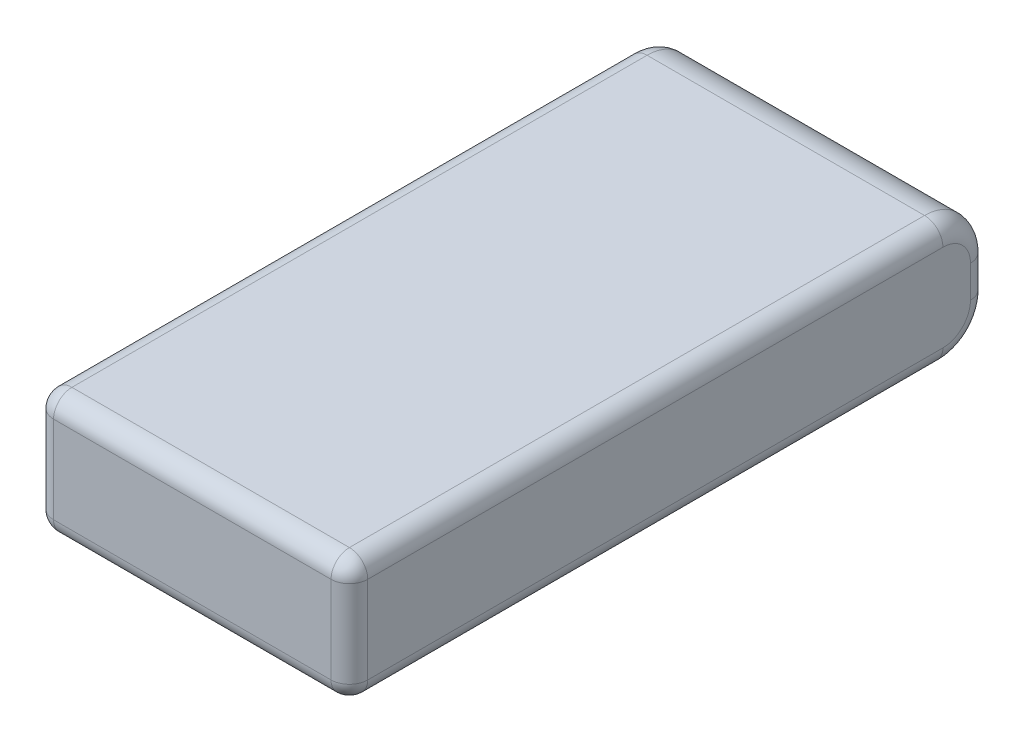
SolidWorks part; units mm, degrees
ref_plane "Front Plane" through (0, 0, 0) normal (0, 0, 1) x (1, 0, 0)
ref_plane "Top Plane" through (0, 0, 0) normal (0, 1, 0) x (1, 0, 0)
ref_plane "Right Plane" through (0, 0, 0) normal (1, 0, 0) x (0, 0, -1)
sketch "Sketch1" plane through (0, 0, 0) normal (0, 1, 0) x (1, 0, 0)
  line L1 (0, 0) -> (34.25, 0)
  line L2 (0, 0) -> (0, 69.7)
  line L3 (0, 69.7) -> (34.25, 69.7)
  line L4 (34.25, 0) -> (34.25, 69.7)
  dimension "D1" = 69.7
  dimension "D2" = 34.25
extrude "Boss-Extrude1" add sketch "Sketch1" along normal blind 13.5
fillet "Fillet1" radius 5 2 edges at (17.125, 0, -69.7) (17.125, 13.5, -69.7)
fillet "Fillet2" radius 2 14 edges at (34.25, 0, -32.35) (34.25, 1.4645, -68.2355) (34.25, 6.75, -69.7) (34.25, 12.0355, -68.2355) (0, 12.0355, -68.2355) (0, 13.5, -32.35) (0, 0, -32.35) (0, 1.4645, -68.2355) (0, 6.75, -69.7) (0, 6.75, 0) (17.125, 13.5, 0) (34.25, 6.75, 0) (17.125, 0, 0) (34.25, 13.5, -32.35)
